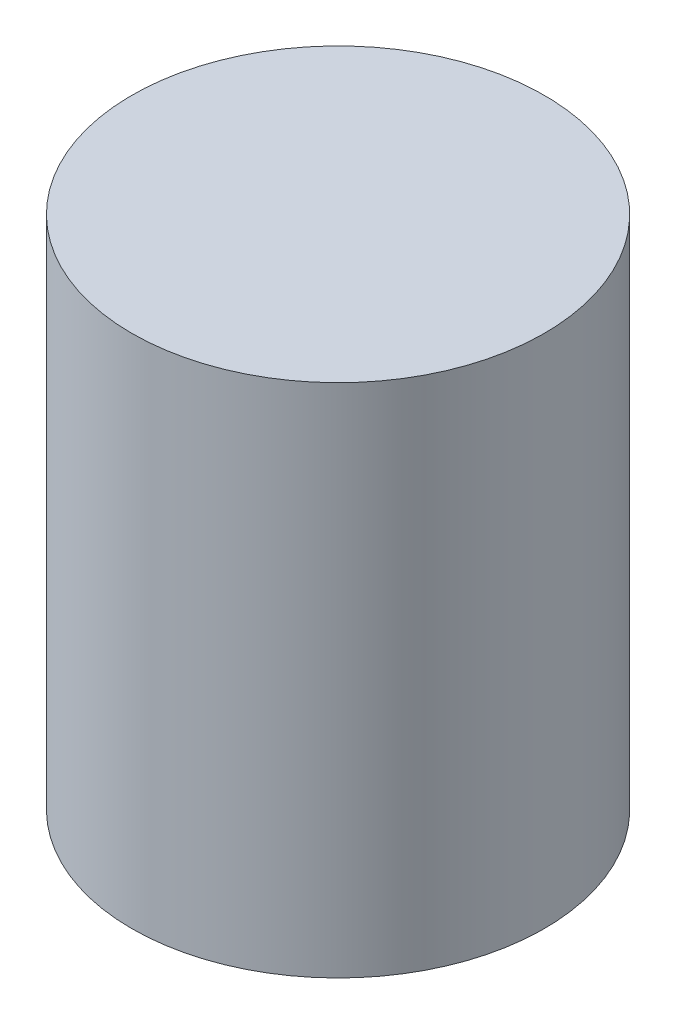
SolidWorks part; units mm, degrees
ref_plane "Front Plane" through (0, 0, 0) normal (0, 0, 1) x (1, 0, 0)
ref_plane "Top Plane" through (0, 0, 0) normal (0, 1, 0) x (1, 0, 0)
ref_plane "Right Plane" through (0, 0, 0) normal (1, 0, 0) x (0, 0, -1)
sketch "Sketch1" plane through (0, 0, 0) normal (0, 1, 0) x (1, 0, 0)
  circle A0 centre (0, 0) radius 4
  dimension "D1" = 8
extrude "Boss-Extrude1" add sketch "Sketch1" along normal blind 10
